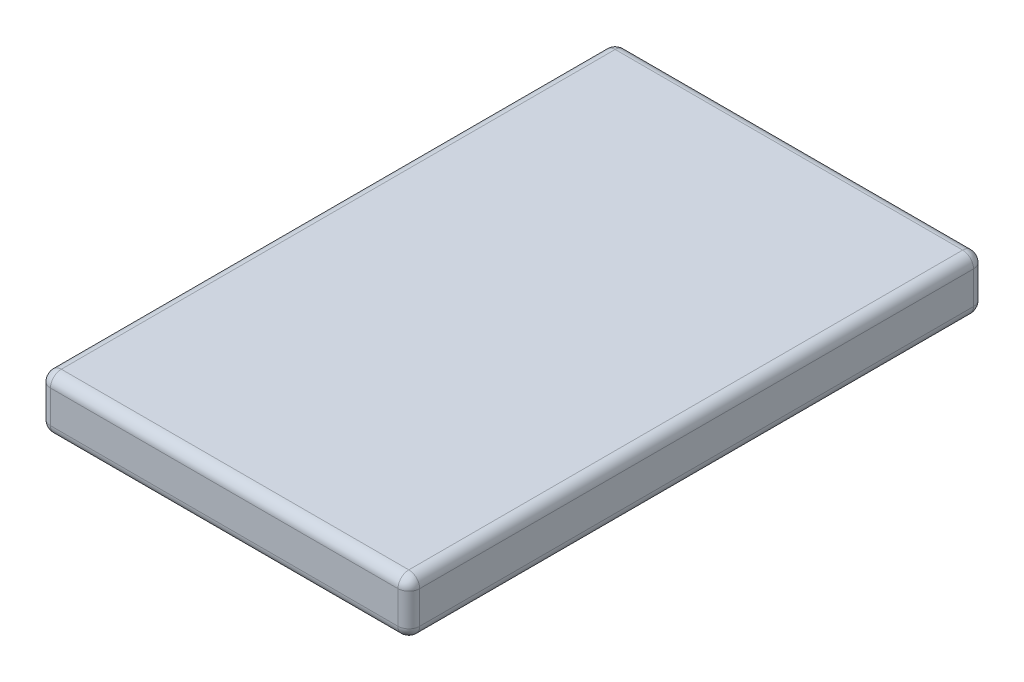
SolidWorks part; units mm, degrees
ref_plane "Front Plane" through (0, 0, 0) normal (0, 0, 1) x (1, 0, 0)
ref_plane "Top Plane" through (0, 0, 0) normal (0, 1, 0) x (1, 0, 0)
ref_plane "Right Plane" through (0, 0, 0) normal (1, 0, 0) x (0, 0, -1)
sketch "Sketch1" plane through (0, 0, 0) normal (0, 1, 0) x (1, 0, 0)
  line L1 (-17, 26.5) -> (17, 26.5)
  line L2 (-17, 26.5) -> (-17, -26.5)
  line L3 (-17, -26.5) -> (17, -26.5)
  line L4 (17, 26.5) -> (17, -26.5)
  line L5 (-17, 26.5) -> (17, -26.5) construction
  line L6 (-17, -26.5) -> (17, 26.5) construction
  point P0 (0, 0)
  dimension "D1" = 53
  dimension "D2" = 34
extrude "Boss-Extrude1" add sketch "Sketch1" along normal blind 5
fillet "Fillet1" radius 1 4 edges at (-17, 0, 0) (-17, 5, 0) (17, 0, 0) (17, 5, 0)
fillet "Fillet2" radius 1 16 edges at (-16.7071, 4.7071, 26.5) (0, 5, 26.5) (16.7071, 4.7071, 26.5) (17, 2.5, 26.5) (16.7071, 0.2929, 26.5) (0, 0, 26.5) (-16.7071, 0.2929, 26.5) (-17, 2.5, 26.5) (16.7071, 0.2929, -26.5) (17, 2.5, -26.5) (16.7071, 4.7071, -26.5) (0, 5, -26.5) (-16.7071, 4.7071, -26.5) (-17, 2.5, -26.5) (-16.7071, 0.2929, -26.5) (0, 0, -26.5)
